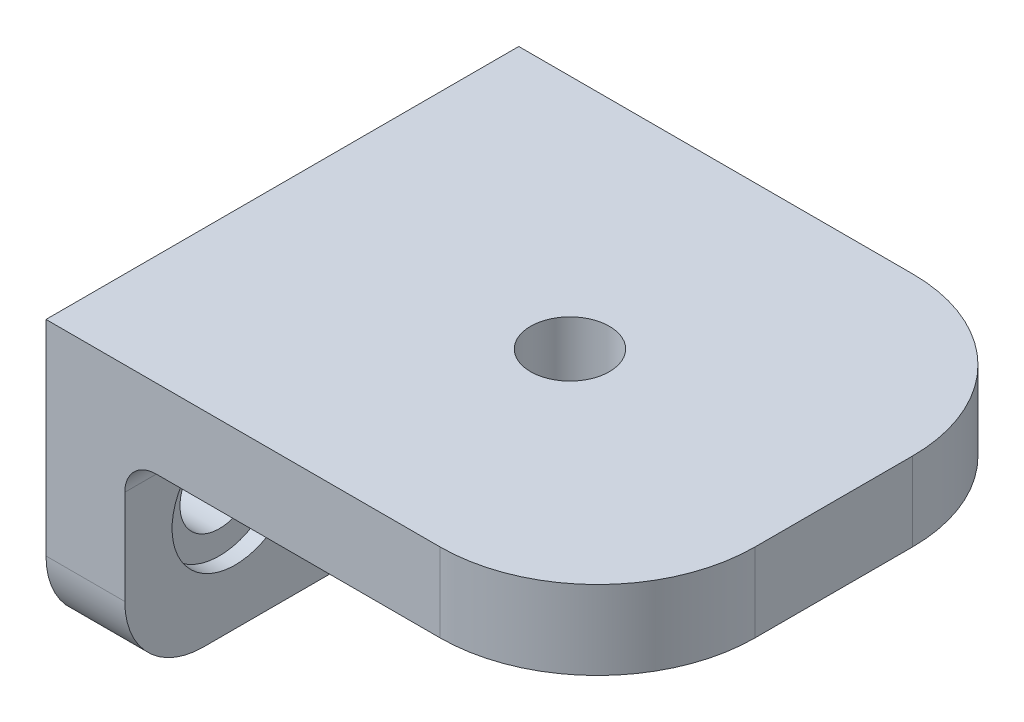
SolidWorks part; units mm, degrees
ref_plane "Front Plane" through (0, 0, 0) normal (0, 0, 1) x (1, 0, 0)
ref_plane "Top Plane" through (0, 0, 0) normal (0, 1, 0) x (1, 0, 0)
ref_plane "Right Plane" through (0, 0, 0) normal (1, 0, 0) x (0, 0, -1)
sketch "Sketch1" plane through (0, 0, 0) normal (0, 1, 0) x (1, 0, 0)
  line L1 (15, -15) -> (-15, -15)
  line L2 (15, -15) -> (15, 15)
  line L3 (15, 15) -> (-15, 15)
  line L4 (-15, -15) -> (-15, 15)
  line L5 (15, -15) -> (-15, 15) construction
  line L6 (15, 15) -> (-15, -15) construction
  point P0 (0, 0)
  dimension "D1" = 30
  dimension "D2" = 30
extrude "Boss-Extrude1" add sketch "Sketch1" along normal blind 5
sketch "Sketch2" plane through (-15, 0, 0) normal (-1, 0, 0) x (0, 0, 1)
  line L0 (15, 5) -> (15, 0) construction
  line L1 (-15, 5) -> (15, 5)
  line L2 (-15, 5) -> (-15, -13)
  line L3 (-15, -13) -> (15, -13)
  line L4 (15, 5) -> (15, -13)
  dimension "D1" = 0
  dimension "D2" = 18
extrude "Boss-Extrude2" add sketch "Sketch2" along normal blind 5
sketch "Sketch3" plane through (-15, 0, 0) normal (1, 0, 0) x (0, 0, -1)
  line L0 (15, -13) -> (-15, -13) construction
  circle A0 centre (-8, -5.5) radius 4
  circle A1 centre (8, -5.5) radius 4
  point P6 (0, -13)
  dimension "D1" = 8
  dimension "D2" = 8
  dimension "D3" = 7.5
  dimension "D4" = 7.5
extrude "Cut-Extrude1" cut sketch "Sketch3" against normal blind 1
sketch "Sketch4" plane through (-16, 0, 0) normal (1, 0, 0) x (0, 0, -1)
  circle A0 centre (-8, -5.5) radius 2.5
  circle A1 centre (8, -5.5) radius 2.5
extrude "Cut-Extrude2" cut sketch "Sketch4" against normal blind 5
sketch "Sketch5" plane through (0, 5, 0) normal (0, 1, 0) x (1, 0, 0)
  line L0 (-20, -15) -> (-20, 15) construction
  circle A0 centre (-1.75, 0) radius 2.5
  dimension "D1" = 18.25
extrude "Cut-Extrude3" cut sketch "Sketch5" against normal blind 5
fillet "Fillet1" radius 10 2 edges at (15, 2.5, -15) (15, 2.5, 15)
fillet "Fillet2" radius 2 1 edges at (-15, 0, 0)
fillet "Fillet3" radius 5 2 edges at (-17.5, -13, -15) (-17.5, -13, 15)
